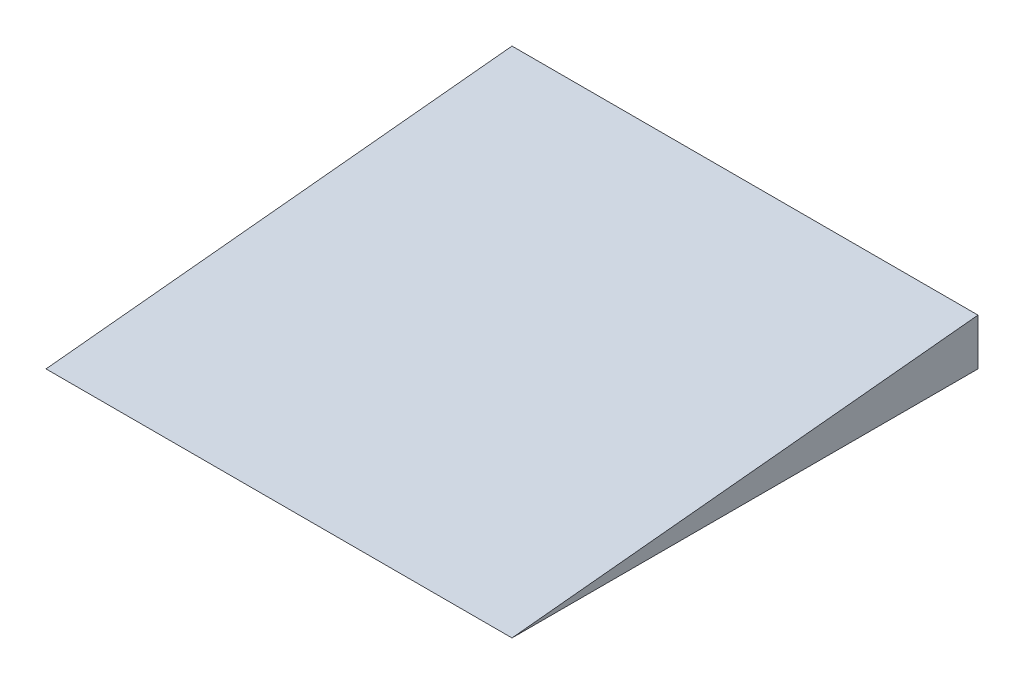
SolidWorks part; units mm, degrees
ref_plane "Front Plane" through (0, 0, 0) normal (0, 0, 1) x (1, 0, 0)
ref_plane "Top Plane" through (0, 0, 0) normal (0, 1, 0) x (1, 0, 0)
ref_plane "Right Plane" through (0, 0, 0) normal (1, 0, 0) x (0, 0, -1)
sketch "Sketch2" plane through (0, 0, 0) normal (0, 1, 0) x (1, 0, 0)
  line L1 (0, 0) -> (1000, 0)
  line L2 (0, 0) -> (0, 1000)
  line L3 (0, 1000) -> (1000, 1000)
  line L4 (1000, 0) -> (1000, 1000)
extrude "Boss-Extrude1" add sketch "Sketch2" along normal blind 100
sketch "Sketch3" plane through (1000, 0, 0) normal (1, 0, 0) x (0, 0, -1)
  line L0 (0, 0) -> (1000, 100)
  line L1 (0, 0) -> (0, 100)
  line L2 (0, 100) -> (1000, 100)
  point P4 (0, 100)
extrude "Cut-Extrude1" cut sketch "Sketch3" against normal blind 1202
